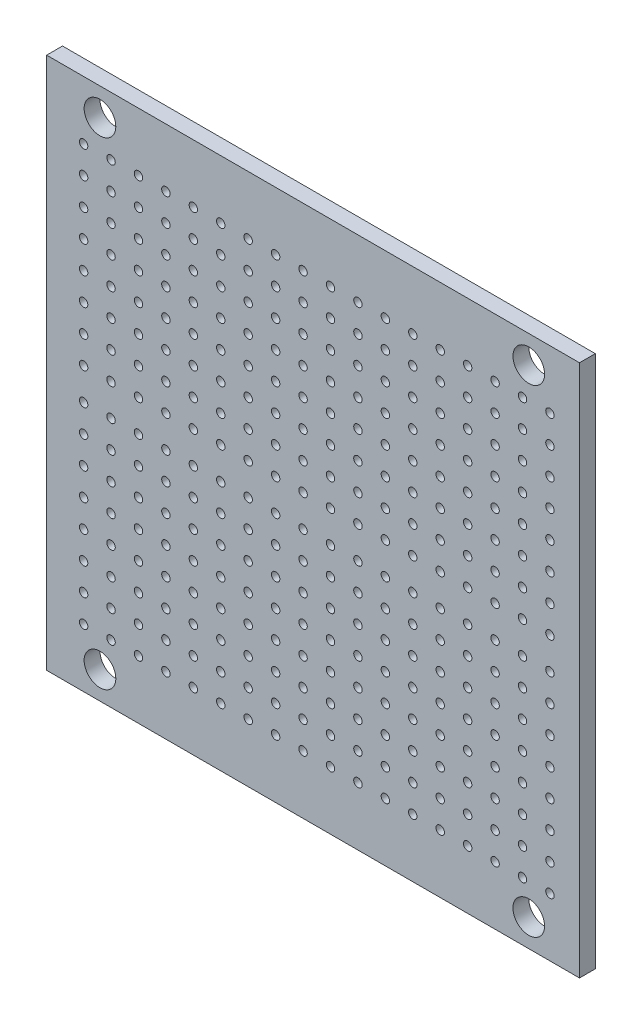
SolidWorks part; units mm, degrees
ref_plane "Front Plane" through (0, 0, 0) normal (0, 0, 1) x (1, 0, 0)
ref_plane "Top Plane" through (0, 0, 0) normal (0, 1, 0) x (1, 0, 0)
ref_plane "Right Plane" through (0, 0, 0) normal (1, 0, 0) x (0, 0, -1)
sketch "Sketch1" plane through (0, 0, 0) normal (0, 0, 1) x (1, 0, 0)
  line L0 (0, 0) -> (25.5, 0) construction
  line L2 (-25, -25.25) -> (-25, 25.25)
  line L3 (-25, 25.25) -> (25.5, 25.25)
  line L4 (25.5, -25.25) -> (25.5, 25.25)
  line L5 (0, 0) -> (-25, 0) construction
  line L6 (-25, -25.25) -> (25.5, -25.25)
  circle A0 centre (-19.95, 22.65) radius 1.5
  circle A1 centre (20.6923, 22.65) radius 1.5
  circle A4 centre (22.7, 19.71) radius 0.4
  circle A5 centre (20.1, 19.71) radius 0.4
  circle A6 centre (17.5, 19.71) radius 0.4
  circle A7 centre (14.9, 19.71) radius 0.4
  circle A8 centre (12.3, 19.71) radius 0.4
  circle A9 centre (9.7, 19.71) radius 0.4
  circle A10 centre (7.1, 19.71) radius 0.4
  circle A11 centre (4.5, 19.71) radius 0.4
  circle A12 centre (1.9, 19.71) radius 0.4
  circle A13 centre (-0.7, 19.71) radius 0.4
  circle A14 centre (-3.3, 19.71) radius 0.4
  circle A15 centre (-5.9, 19.71) radius 0.4
  circle A16 centre (-8.5, 19.71) radius 0.4
  circle A17 centre (-11.1, 19.71) radius 0.4
  circle A18 centre (-13.7, 19.71) radius 0.4
  circle A19 centre (-16.3, 19.71) radius 0.4
  circle A20 centre (-18.9, 19.71) radius 0.4
  circle A21 centre (-21.5, 19.71) radius 0.4
  circle A22 centre (20.1, 17.11) radius 0.4
  circle A23 centre (17.5, 17.11) radius 0.4
  circle A24 centre (14.9, 17.11) radius 0.4
  circle A25 centre (12.3, 17.11) radius 0.4
  circle A26 centre (9.7, 17.11) radius 0.4
  circle A27 centre (7.1, 17.11) radius 0.4
  circle A28 centre (4.5, 17.11) radius 0.4
  circle A29 centre (1.9, 17.11) radius 0.4
  circle A30 centre (-0.7, 17.11) radius 0.4
  circle A31 centre (-3.3, 17.11) radius 0.4
  circle A32 centre (-5.9, 17.11) radius 0.4
  circle A33 centre (-8.5, 17.11) radius 0.4
  circle A34 centre (-11.1, 17.11) radius 0.4
  circle A35 centre (-13.7, 17.11) radius 0.4
  circle A36 centre (-16.3, 17.11) radius 0.4
  circle A37 centre (-18.9, 17.11) radius 0.4
  circle A38 centre (-21.5, 17.11) radius 0.4
  circle A39 centre (20.1, 14.51) radius 0.4
  circle A40 centre (17.5, 14.51) radius 0.4
  circle A41 centre (14.9, 14.51) radius 0.4
  circle A42 centre (12.3, 14.51) radius 0.4
  circle A43 centre (9.7, 14.51) radius 0.4
  circle A44 centre (7.1, 14.51) radius 0.4
  circle A45 centre (4.5, 14.51) radius 0.4
  circle A46 centre (1.9, 14.51) radius 0.4
  circle A47 centre (-0.7, 14.51) radius 0.4
  circle A48 centre (-3.3, 14.51) radius 0.4
  circle A49 centre (-5.9, 14.51) radius 0.4
  circle A50 centre (-8.5, 14.51) radius 0.4
  circle A51 centre (-11.1, 14.51) radius 0.4
  circle A52 centre (-13.7, 14.51) radius 0.4
  circle A53 centre (-16.3, 14.51) radius 0.4
  circle A54 centre (-18.9, 14.51) radius 0.4
  circle A55 centre (-21.5, 14.51) radius 0.4
  circle A56 centre (20.1, 11.91) radius 0.4
  circle A57 centre (17.5, 11.91) radius 0.4
  circle A58 centre (14.9, 11.91) radius 0.4
  circle A59 centre (12.3, 11.91) radius 0.4
  circle A60 centre (9.7, 11.91) radius 0.4
  circle A61 centre (7.1, 11.91) radius 0.4
  circle A62 centre (4.5, 11.91) radius 0.4
  circle A63 centre (1.9, 11.91) radius 0.4
  circle A64 centre (-0.7, 11.91) radius 0.4
  circle A65 centre (-3.3, 11.91) radius 0.4
  circle A66 centre (-5.9, 11.91) radius 0.4
  circle A67 centre (-8.5, 11.91) radius 0.4
  circle A68 centre (-11.1, 11.91) radius 0.4
  circle A69 centre (-13.7, 11.91) radius 0.4
  circle A70 centre (-16.3, 11.91) radius 0.4
  circle A71 centre (-18.9, 11.91) radius 0.4
  circle A72 centre (-21.5, 11.91) radius 0.4
  circle A73 centre (20.1, 9.31) radius 0.4
  circle A74 centre (17.5, 9.31) radius 0.4
  circle A75 centre (14.9, 9.31) radius 0.4
  circle A76 centre (12.3, 9.31) radius 0.4
  circle A77 centre (9.7, 9.31) radius 0.4
  circle A78 centre (7.1, 9.31) radius 0.4
  circle A79 centre (4.5, 9.31) radius 0.4
  circle A80 centre (1.9, 9.31) radius 0.4
  circle A81 centre (-0.7, 9.31) radius 0.4
  circle A82 centre (-3.3, 9.31) radius 0.4
  circle A83 centre (-5.9, 9.31) radius 0.4
  circle A84 centre (-8.5, 9.31) radius 0.4
  circle A85 centre (-11.1, 9.31) radius 0.4
  circle A86 centre (-13.7, 9.31) radius 0.4
  circle A87 centre (-16.3, 9.31) radius 0.4
  circle A88 centre (-18.9, 9.31) radius 0.4
  circle A89 centre (-21.5, 9.31) radius 0.4
  circle A90 centre (20.1, 6.71) radius 0.4
  circle A91 centre (17.5, 6.71) radius 0.4
  circle A92 centre (14.9, 6.71) radius 0.4
  circle A93 centre (12.3, 6.71) radius 0.4
  circle A94 centre (9.7, 6.71) radius 0.4
  circle A95 centre (7.1, 6.71) radius 0.4
  circle A96 centre (4.5, 6.71) radius 0.4
  circle A97 centre (1.9, 6.71) radius 0.4
  circle A98 centre (-0.7, 6.71) radius 0.4
  circle A99 centre (-3.3, 6.71) radius 0.4
  circle A100 centre (-5.9, 6.71) radius 0.4
  circle A101 centre (-8.5, 6.71) radius 0.4
  circle A102 centre (-11.1, 6.71) radius 0.4
  circle A103 centre (-13.7, 6.71) radius 0.4
  circle A104 centre (-16.3, 6.71) radius 0.4
  circle A105 centre (-18.9, 6.71) radius 0.4
  circle A106 centre (-21.5, 6.71) radius 0.4
  circle A107 centre (20.1, 4.11) radius 0.4
  circle A108 centre (17.5, 4.11) radius 0.4
  circle A109 centre (14.9, 4.11) radius 0.4
  circle A110 centre (12.3, 4.11) radius 0.4
  circle A111 centre (9.7, 4.11) radius 0.4
  circle A112 centre (7.1, 4.11) radius 0.4
  circle A113 centre (4.5, 4.11) radius 0.4
  circle A114 centre (1.9, 4.11) radius 0.4
  circle A115 centre (-0.7, 4.11) radius 0.4
  circle A116 centre (-3.3, 4.11) radius 0.4
  circle A117 centre (-5.9, 4.11) radius 0.4
  circle A118 centre (-8.5, 4.11) radius 0.4
  circle A119 centre (-11.1, 4.11) radius 0.4
  circle A120 centre (-13.7, 4.11) radius 0.4
  circle A121 centre (-16.3, 4.11) radius 0.4
  circle A122 centre (-18.9, 4.11) radius 0.4
  circle A123 centre (-21.5, 4.11) radius 0.4
  circle A124 centre (20.1, 1.51) radius 0.4
  circle A125 centre (17.5, 1.51) radius 0.4
  circle A126 centre (14.9, 1.51) radius 0.4
  circle A127 centre (12.3, 1.51) radius 0.4
  circle A128 centre (9.7, 1.51) radius 0.4
  circle A129 centre (7.1, 1.51) radius 0.4
  circle A130 centre (4.5, 1.51) radius 0.4
  circle A131 centre (1.9, 1.51) radius 0.4
  circle A132 centre (-0.7, 1.51) radius 0.4
  circle A133 centre (-3.3, 1.51) radius 0.4
  circle A134 centre (-5.9, 1.51) radius 0.4
  circle A135 centre (-8.5, 1.51) radius 0.4
  circle A136 centre (-11.1, 1.51) radius 0.4
  circle A137 centre (-13.7, 1.51) radius 0.4
  circle A138 centre (-16.3, 1.51) radius 0.4
  circle A139 centre (-18.9, 1.51) radius 0.4
  circle A140 centre (-21.5, 1.51) radius 0.4
  circle A413 centre (22.7, 17.11) radius 0.4
  circle A414 centre (22.7, 14.51) radius 0.4
  circle A415 centre (22.7, 11.91) radius 0.4
  circle A416 centre (22.7, 9.31) radius 0.4
  circle A417 centre (22.7, 6.71) radius 0.4
  circle A418 centre (22.7, 4.11) radius 0.4
  circle A419 centre (22.7, 1.51) radius 0.4
  circle A436 centre (-18.9, -27.09) radius 0.4 [skipped]
  circle A437 centre (-21.5, -27.09) radius 0.4 [skipped]
  circle A438 centre (20.1, -29.69) radius 0.4 [skipped]
  circle A439 centre (17.5, -29.69) radius 0.4 [skipped]
  circle A440 centre (14.9, -29.69) radius 0.4 [skipped]
  circle A441 centre (12.3, -29.69) radius 0.4 [skipped]
  circle A442 centre (9.7, -29.69) radius 0.4 [skipped]
  circle A443 centre (7.1, -29.69) radius 0.4 [skipped]
  circle A444 centre (4.5, -29.69) radius 0.4 [skipped]
  circle A445 centre (1.9, -29.69) radius 0.4 [skipped]
  circle A446 centre (-0.7, -29.69) radius 0.4 [skipped]
  circle A447 centre (-3.3, -29.69) radius 0.4 [skipped]
  circle A448 centre (-5.9, -29.69) radius 0.4 [skipped]
  circle A449 centre (-8.5, -29.69) radius 0.4 [skipped]
  circle A450 centre (-11.1, -29.69) radius 0.4 [skipped]
  circle A451 centre (-13.7, -29.69) radius 0.4 [skipped]
  circle A452 centre (-16.3, -29.69) radius 0.4 [skipped]
  circle A453 centre (-18.9, -29.69) radius 0.4 [skipped]
  circle A454 centre (-21.5, -29.69) radius 0.4 [skipped]
  circle A455 centre (20.1, -32.29) radius 0.4 [skipped]
  circle A456 centre (17.5, -32.29) radius 0.4 [skipped]
  circle A457 centre (14.9, -32.29) radius 0.4 [skipped]
  circle A458 centre (12.3, -32.29) radius 0.4 [skipped]
  circle A459 centre (9.7, -32.29) radius 0.4 [skipped]
  circle A460 centre (7.1, -32.29) radius 0.4 [skipped]
  circle A461 centre (4.5, -32.29) radius 0.4 [skipped]
  circle A462 centre (1.9, -32.29) radius 0.4 [skipped]
  circle A463 centre (-0.7, -32.29) radius 0.4 [skipped]
  circle A464 centre (-3.3, -32.29) radius 0.4 [skipped]
  circle A465 centre (-5.9, -32.29) radius 0.4 [skipped]
  circle A466 centre (-8.5, -32.29) radius 0.4 [skipped]
  circle A467 centre (-11.1, -32.29) radius 0.4 [skipped]
  circle A468 centre (-13.7, -32.29) radius 0.4 [skipped]
  circle A469 centre (-16.3, -32.29) radius 0.4 [skipped]
  circle A470 centre (-18.9, -32.29) radius 0.4 [skipped]
  circle A471 centre (-21.5, -32.29) radius 0.4 [skipped]
  circle A472 centre (20.1, -34.89) radius 0.4 [skipped]
  circle A473 centre (17.5, -34.89) radius 0.4 [skipped]
  circle A474 centre (14.9, -34.89) radius 0.4 [skipped]
  circle A475 centre (12.3, -34.89) radius 0.4 [skipped]
  circle A476 centre (9.7, -34.89) radius 0.4 [skipped]
  circle A477 centre (7.1, -34.89) radius 0.4 [skipped]
  circle A478 centre (4.5, -34.89) radius 0.4 [skipped]
  circle A479 centre (1.9, -34.89) radius 0.4 [skipped]
  circle A480 centre (-0.7, -34.89) radius 0.4 [skipped]
  circle A481 centre (-3.3, -34.89) radius 0.4 [skipped]
  circle A482 centre (-5.9, -34.89) radius 0.4 [skipped]
  circle A483 centre (-8.5, -34.89) radius 0.4 [skipped]
  circle A484 centre (-11.1, -34.89) radius 0.4 [skipped]
  circle A485 centre (-13.7, -34.89) radius 0.4 [skipped]
  circle A486 centre (-16.3, -34.89) radius 0.4 [skipped]
  circle A487 centre (-18.9, -34.89) radius 0.4 [skipped]
  circle A488 centre (-21.5, -34.89) radius 0.4 [skipped]
  circle A489 centre (20.1, -37.49) radius 0.4 [skipped]
  circle A490 centre (17.5, -37.49) radius 0.4 [skipped]
  circle A491 centre (14.9, -37.49) radius 0.4 [skipped]
  circle A492 centre (12.3, -37.49) radius 0.4 [skipped]
  circle A493 centre (9.7, -37.49) radius 0.4 [skipped]
  circle A494 centre (7.1, -37.49) radius 0.4 [skipped]
  circle A495 centre (4.5, -37.49) radius 0.4 [skipped]
  circle A496 centre (1.9, -37.49) radius 0.4 [skipped]
  circle A497 centre (-0.7, -37.49) radius 0.4 [skipped]
  circle A498 centre (-3.3, -37.49) radius 0.4 [skipped]
  circle A499 centre (-5.9, -37.49) radius 0.4 [skipped]
  circle A500 centre (-8.5, -37.49) radius 0.4 [skipped]
  circle A501 centre (-11.1, -37.49) radius 0.4 [skipped]
  circle A502 centre (-13.7, -37.49) radius 0.4 [skipped]
  circle A503 centre (-16.3, -37.49) radius 0.4 [skipped]
  circle A504 centre (-18.9, -37.49) radius 0.4 [skipped]
  circle A505 centre (-21.5, -37.49) radius 0.4 [skipped]
  circle A506 centre (20.1, -40.09) radius 0.4 [skipped]
  circle A507 centre (17.5, -40.09) radius 0.4 [skipped]
  circle A508 centre (14.9, -40.09) radius 0.4 [skipped]
  circle A509 centre (12.3, -40.09) radius 0.4 [skipped]
  circle A510 centre (9.7, -40.09) radius 0.4 [skipped]
  circle A511 centre (7.1, -40.09) radius 0.4 [skipped]
  circle A512 centre (4.5, -40.09) radius 0.4 [skipped]
  circle A513 centre (1.9, -40.09) radius 0.4 [skipped]
  circle A514 centre (-0.7, -40.09) radius 0.4 [skipped]
  circle A515 centre (22.7, -29.69) radius 0.4 [skipped]
  circle A516 centre (22.7, -32.29) radius 0.4 [skipped]
  circle A517 centre (22.7, -34.89) radius 0.4 [skipped]
  circle A518 centre (22.7, -37.49) radius 0.4 [skipped]
  circle A519 centre (22.7, -40.09) radius 0.4 [skipped]
  circle A520 centre (-3.3, -40.09) radius 0.4 [skipped]
  circle A521 centre (-5.9, -40.09) radius 0.4 [skipped]
  circle A522 centre (-8.5, -40.09) radius 0.4 [skipped]
  circle A523 centre (-11.1, -40.09) radius 0.4 [skipped]
  circle A524 centre (-13.7, -40.09) radius 0.4 [skipped]
  circle A525 centre (-16.3, -40.09) radius 0.4 [skipped]
  circle A526 centre (-18.9, -40.09) radius 0.4 [skipped]
  circle A527 centre (-21.5, -40.09) radius 0.4 [skipped]
  circle A528 centre (20.1, -27.09) radius 0.4 [skipped]
  circle A529 centre (17.5, -27.09) radius 0.4 [skipped]
  circle A530 centre (14.9, -27.09) radius 0.4 [skipped]
  circle A531 centre (12.3, -27.09) radius 0.4 [skipped]
  circle A532 centre (9.7, -27.09) radius 0.4 [skipped]
  circle A533 centre (7.1, -27.09) radius 0.4 [skipped]
  circle A534 centre (4.5, -27.09) radius 0.4 [skipped]
  circle A535 centre (1.9, -27.09) radius 0.4 [skipped]
  circle A536 centre (-0.7, -27.09) radius 0.4 [skipped]
  circle A537 centre (-3.3, -27.09) radius 0.4 [skipped]
  circle A538 centre (-5.9, -27.09) radius 0.4 [skipped]
  circle A539 centre (-8.5, -27.09) radius 0.4 [skipped]
  circle A540 centre (-11.1, -27.09) radius 0.4 [skipped]
  circle A541 centre (-13.7, -27.09) radius 0.4 [skipped]
  circle A542 centre (-16.3, -27.09) radius 0.4 [skipped]
  circle A543 centre (22.7, -27.09) radius 0.4 [skipped]
  circle A544 centre (20.1, -1.09) radius 0.4 [skipped]
  circle A545 centre (17.5, -1.09) radius 0.4 [skipped]
  circle A546 centre (14.9, -1.09) radius 0.4 [skipped]
  circle A547 centre (12.3, -1.09) radius 0.4 [skipped]
  circle A548 centre (9.7, -1.09) radius 0.4 [skipped]
  circle A549 centre (7.1, -1.09) radius 0.4 [skipped]
  circle A550 centre (4.5, -1.09) radius 0.4 [skipped]
  circle A551 centre (1.9, -1.09) radius 0.4 [skipped]
  circle A552 centre (-0.7, -1.09) radius 0.4 [skipped]
  circle A553 centre (-3.3, -1.09) radius 0.4 [skipped]
  circle A554 centre (-5.9, -1.09) radius 0.4 [skipped]
  circle A555 centre (-8.5, -1.09) radius 0.4 [skipped]
  circle A556 centre (-11.1, -1.09) radius 0.4 [skipped]
  circle A557 centre (-13.7, -1.09) radius 0.4 [skipped]
  circle A558 centre (-16.3, -1.09) radius 0.4 [skipped]
  circle A559 centre (-18.9, -1.09) radius 0.4 [skipped]
  circle A560 centre (-21.5, -1.09) radius 0.4 [skipped]
  circle A561 centre (20.1, -3.69) radius 0.4 [skipped]
  circle A562 centre (17.5, -3.69) radius 0.4 [skipped]
  circle A563 centre (14.9, -3.69) radius 0.4 [skipped]
  circle A564 centre (12.3, -3.69) radius 0.4 [skipped]
  circle A565 centre (9.7, -3.69) radius 0.4 [skipped]
  circle A566 centre (7.1, -3.69) radius 0.4 [skipped]
  circle A567 centre (4.5, -3.69) radius 0.4 [skipped]
  circle A568 centre (1.9, -3.69) radius 0.4 [skipped]
  circle A569 centre (-0.7, -3.69) radius 0.4 [skipped]
  circle A570 centre (-3.3, -3.69) radius 0.4 [skipped]
  circle A571 centre (-5.9, -3.69) radius 0.4 [skipped]
  circle A572 centre (-8.5, -3.69) radius 0.4 [skipped]
  circle A573 centre (-11.1, -3.69) radius 0.4 [skipped]
  circle A574 centre (-13.7, -3.69) radius 0.4 [skipped]
  circle A575 centre (-16.3, -3.69) radius 0.4 [skipped]
  circle A576 centre (-18.9, -3.69) radius 0.4 [skipped]
  circle A577 centre (-21.5, -3.69) radius 0.4 [skipped]
  circle A578 centre (20.1, -6.29) radius 0.4 [skipped]
  circle A579 centre (17.5, -6.29) radius 0.4 [skipped]
  circle A580 centre (14.9, -6.29) radius 0.4 [skipped]
  circle A581 centre (12.3, -6.29) radius 0.4 [skipped]
  circle A582 centre (9.7, -6.29) radius 0.4 [skipped]
  circle A583 centre (7.1, -6.29) radius 0.4 [skipped]
  circle A584 centre (4.5, -6.29) radius 0.4 [skipped]
  circle A585 centre (1.9, -6.29) radius 0.4 [skipped]
  circle A586 centre (-0.7, -6.29) radius 0.4 [skipped]
  circle A587 centre (-3.3, -6.29) radius 0.4 [skipped]
  circle A588 centre (-5.9, -6.29) radius 0.4 [skipped]
  circle A589 centre (-8.5, -6.29) radius 0.4 [skipped]
  circle A590 centre (-11.1, -6.29) radius 0.4 [skipped]
  circle A591 centre (-13.7, -6.29) radius 0.4 [skipped]
  circle A592 centre (-16.3, -6.29) radius 0.4 [skipped]
  circle A593 centre (-18.9, -6.29) radius 0.4 [skipped]
  circle A594 centre (-21.5, -6.29) radius 0.4 [skipped]
  circle A595 centre (20.1, -8.89) radius 0.4 [skipped]
  circle A596 centre (17.5, -8.89) radius 0.4 [skipped]
  circle A597 centre (14.9, -8.89) radius 0.4 [skipped]
  circle A598 centre (12.3, -8.89) radius 0.4 [skipped]
  circle A599 centre (9.7, -8.89) radius 0.4 [skipped]
  circle A600 centre (7.1, -8.89) radius 0.4 [skipped]
  circle A601 centre (4.5, -8.89) radius 0.4 [skipped]
  circle A602 centre (1.9, -8.89) radius 0.4 [skipped]
  circle A603 centre (-0.7, -8.89) radius 0.4 [skipped]
  circle A604 centre (-3.3, -8.89) radius 0.4 [skipped]
  circle A605 centre (-5.9, -8.89) radius 0.4 [skipped]
  circle A606 centre (-8.5, -8.89) radius 0.4 [skipped]
  circle A607 centre (-11.1, -8.89) radius 0.4 [skipped]
  circle A608 centre (-13.7, -8.89) radius 0.4 [skipped]
  circle A609 centre (-16.3, -8.89) radius 0.4 [skipped]
  circle A610 centre (-18.9, -8.89) radius 0.4 [skipped]
  circle A611 centre (-21.5, -8.89) radius 0.4 [skipped]
  circle A612 centre (20.1, -11.49) radius 0.4 [skipped]
  circle A613 centre (17.5, -11.49) radius 0.4 [skipped]
  circle A614 centre (14.9, -11.49) radius 0.4 [skipped]
  circle A615 centre (12.3, -11.49) radius 0.4 [skipped]
  circle A616 centre (9.7, -11.49) radius 0.4 [skipped]
  circle A617 centre (7.1, -11.49) radius 0.4 [skipped]
  circle A618 centre (4.5, -11.49) radius 0.4 [skipped]
  circle A619 centre (1.9, -11.49) radius 0.4 [skipped]
  circle A620 centre (-0.7, -11.49) radius 0.4 [skipped]
  circle A621 centre (-3.3, -11.49) radius 0.4 [skipped]
  circle A622 centre (-5.9, -11.49) radius 0.4 [skipped]
  circle A623 centre (-8.5, -11.49) radius 0.4 [skipped]
  circle A624 centre (-11.1, -11.49) radius 0.4 [skipped]
  circle A625 centre (-13.7, -11.49) radius 0.4 [skipped]
  circle A626 centre (-16.3, -11.49) radius 0.4 [skipped]
  circle A627 centre (-18.9, -11.49) radius 0.4 [skipped]
  circle A628 centre (-21.5, -11.49) radius 0.4 [skipped]
  circle A629 centre (20.1, -14.09) radius 0.4 [skipped]
  circle A630 centre (17.5, -14.09) radius 0.4 [skipped]
  circle A631 centre (14.9, -14.09) radius 0.4 [skipped]
  circle A632 centre (12.3, -14.09) radius 0.4 [skipped]
  circle A633 centre (9.7, -14.09) radius 0.4 [skipped]
  circle A634 centre (7.1, -14.09) radius 0.4 [skipped]
  circle A635 centre (4.5, -14.09) radius 0.4 [skipped]
  circle A636 centre (1.9, -14.09) radius 0.4 [skipped]
  circle A637 centre (-0.7, -14.09) radius 0.4 [skipped]
  circle A638 centre (-3.3, -14.09) radius 0.4 [skipped]
  circle A639 centre (-5.9, -14.09) radius 0.4 [skipped]
  circle A640 centre (-8.5, -14.09) radius 0.4 [skipped]
  circle A641 centre (-11.1, -14.09) radius 0.4 [skipped]
  circle A642 centre (-13.7, -14.09) radius 0.4 [skipped]
  circle A643 centre (-16.3, -14.09) radius 0.4 [skipped]
  circle A644 centre (-18.9, -14.09) radius 0.4 [skipped]
  circle A645 centre (-21.5, -14.09) radius 0.4 [skipped]
  circle A646 centre (20.1, -16.69) radius 0.4 [skipped]
  circle A647 centre (17.5, -16.69) radius 0.4 [skipped]
  circle A648 centre (14.9, -16.69) radius 0.4 [skipped]
  circle A649 centre (12.3, -16.69) radius 0.4 [skipped]
  circle A650 centre (9.7, -16.69) radius 0.4 [skipped]
  circle A651 centre (7.1, -16.69) radius 0.4 [skipped]
  circle A652 centre (4.5, -16.69) radius 0.4 [skipped]
  circle A653 centre (1.9, -16.69) radius 0.4 [skipped]
  circle A654 centre (-0.7, -16.69) radius 0.4 [skipped]
  circle A655 centre (-3.3, -16.69) radius 0.4 [skipped]
  circle A656 centre (-5.9, -16.69) radius 0.4 [skipped]
  circle A657 centre (-8.5, -16.69) radius 0.4 [skipped]
  circle A658 centre (-11.1, -16.69) radius 0.4 [skipped]
  circle A659 centre (-13.7, -16.69) radius 0.4 [skipped]
  circle A660 centre (-16.3, -16.69) radius 0.4 [skipped]
  circle A661 centre (-18.9, -16.69) radius 0.4 [skipped]
  circle A662 centre (-21.5, -16.69) radius 0.4 [skipped]
  circle A663 centre (20.1, -19.29) radius 0.4 [skipped]
  circle A664 centre (17.5, -19.29) radius 0.4 [skipped]
  circle A665 centre (14.9, -19.29) radius 0.4 [skipped]
  circle A666 centre (12.3, -19.29) radius 0.4 [skipped]
  circle A667 centre (9.7, -19.29) radius 0.4 [skipped]
  circle A668 centre (7.1, -19.29) radius 0.4 [skipped]
  circle A669 centre (4.5, -19.29) radius 0.4 [skipped]
  circle A670 centre (1.9, -19.29) radius 0.4 [skipped]
  circle A671 centre (-0.7, -19.29) radius 0.4 [skipped]
  circle A672 centre (-3.3, -19.29) radius 0.4 [skipped]
  circle A673 centre (-5.9, -19.29) radius 0.4 [skipped]
  circle A674 centre (-8.5, -19.29) radius 0.4 [skipped]
  circle A675 centre (-11.1, -19.29) radius 0.4 [skipped]
  circle A676 centre (-13.7, -19.29) radius 0.4 [skipped]
  circle A677 centre (-16.3, -19.29) radius 0.4 [skipped]
  circle A678 centre (-18.9, -19.29) radius 0.4 [skipped]
  circle A679 centre (-21.5, -19.29) radius 0.4 [skipped]
  circle A680 centre (20.1, -21.89) radius 0.4 [skipped]
  circle A681 centre (17.5, -21.89) radius 0.4 [skipped]
  circle A682 centre (14.9, -21.89) radius 0.4 [skipped]
  circle A683 centre (12.3, -21.89) radius 0.4 [skipped]
  circle A684 centre (9.7, -21.89) radius 0.4 [skipped]
  circle A685 centre (7.1, -21.89) radius 0.4 [skipped]
  circle A686 centre (4.5, -21.89) radius 0.4 [skipped]
  circle A687 centre (1.9, -21.89) radius 0.4 [skipped]
  circle A688 centre (-0.7, -21.89) radius 0.4 [skipped]
  circle A689 centre (-3.3, -21.89) radius 0.4 [skipped]
  circle A690 centre (-5.9, -21.89) radius 0.4 [skipped]
  circle A691 centre (-8.5, -21.89) radius 0.4 [skipped]
  circle A692 centre (-11.1, -21.89) radius 0.4 [skipped]
  circle A693 centre (-13.7, -21.89) radius 0.4 [skipped]
  circle A694 centre (-16.3, -21.89) radius 0.4 [skipped]
  circle A695 centre (-18.9, -21.89) radius 0.4 [skipped]
  circle A696 centre (-21.5, -21.89) radius 0.4 [skipped]
  circle A697 centre (20.1, -24.49) radius 0.4 [skipped]
  circle A698 centre (17.5, -24.49) radius 0.4 [skipped]
  circle A699 centre (14.9, -24.49) radius 0.4 [skipped]
  circle A700 centre (12.3, -24.49) radius 0.4 [skipped]
  circle A701 centre (9.7, -24.49) radius 0.4 [skipped]
  circle A702 centre (7.1, -24.49) radius 0.4 [skipped]
  circle A703 centre (4.5, -24.49) radius 0.4 [skipped]
  circle A704 centre (1.9, -24.49) radius 0.4 [skipped]
  circle A705 centre (-0.7, -24.49) radius 0.4 [skipped]
  circle A706 centre (-3.3, -24.49) radius 0.4 [skipped]
  circle A707 centre (-5.9, -24.49) radius 0.4 [skipped]
  circle A708 centre (-8.5, -24.49) radius 0.4 [skipped]
  circle A709 centre (-11.1, -24.49) radius 0.4 [skipped]
  circle A710 centre (-13.7, -24.49) radius 0.4 [skipped]
  circle A711 centre (-16.3, -24.49) radius 0.4 [skipped]
  circle A712 centre (-18.9, -24.49) radius 0.4 [skipped]
  circle A713 centre (-21.5, -24.49) radius 0.4 [skipped]
  circle A714 centre (22.7, -1.09) radius 0.4 [skipped]
  circle A715 centre (22.7, -3.69) radius 0.4 [skipped]
  circle A716 centre (22.7, -6.29) radius 0.4 [skipped]
  circle A717 centre (22.7, -8.89) radius 0.4 [skipped]
  circle A718 centre (22.7, -11.49) radius 0.4 [skipped]
  circle A719 centre (22.7, -14.09) radius 0.4 [skipped]
  circle A720 centre (22.7, -16.69) radius 0.4 [skipped]
  circle A721 centre (22.7, -19.29) radius 0.4 [skipped]
  circle A722 centre (22.7, -21.89) radius 0.4 [skipped]
  circle A723 centre (22.7, -24.49) radius 0.4 [skipped]
  circle A724 centre (22.7, -1.51) radius 0.4
  circle A725 centre (22.7, -4.11) radius 0.4
  circle A726 centre (22.7, -6.71) radius 0.4
  circle A727 centre (22.7, -9.31) radius 0.4
  circle A728 centre (22.7, -11.91) radius 0.4
  circle A729 centre (22.7, -14.51) radius 0.4
  circle A730 centre (22.7, -17.11) radius 0.4
  circle A731 centre (-21.5, -1.51) radius 0.4
  circle A732 centre (-18.9, -1.51) radius 0.4
  circle A733 centre (-16.3, -1.51) radius 0.4
  circle A734 centre (-13.7, -1.51) radius 0.4
  circle A735 centre (-11.1, -1.51) radius 0.4
  circle A736 centre (-8.5, -1.51) radius 0.4
  circle A737 centre (-5.9, -1.51) radius 0.4
  circle A738 centre (-3.3, -1.51) radius 0.4
  circle A739 centre (-0.7, -1.51) radius 0.4
  circle A740 centre (1.9, -1.51) radius 0.4
  circle A741 centre (4.5, -1.51) radius 0.4
  circle A742 centre (7.1, -1.51) radius 0.4
  circle A743 centre (9.7, -1.51) radius 0.4
  circle A744 centre (12.3, -1.51) radius 0.4
  circle A745 centre (14.9, -1.51) radius 0.4
  circle A746 centre (17.5, -1.51) radius 0.4
  circle A747 centre (20.1, -1.51) radius 0.4
  circle A748 centre (-21.5, -4.11) radius 0.4
  circle A749 centre (-18.9, -4.11) radius 0.4
  circle A750 centre (-16.3, -4.11) radius 0.4
  circle A751 centre (-13.7, -4.11) radius 0.4
  circle A752 centre (-11.1, -4.11) radius 0.4
  circle A753 centre (-8.5, -4.11) radius 0.4
  circle A754 centre (-5.9, -4.11) radius 0.4
  circle A755 centre (-3.3, -4.11) radius 0.4
  circle A756 centre (-0.7, -4.11) radius 0.4
  circle A757 centre (1.9, -4.11) radius 0.4
  circle A758 centre (4.5, -4.11) radius 0.4
  circle A759 centre (7.1, -4.11) radius 0.4
  circle A760 centre (9.7, -4.11) radius 0.4
  circle A761 centre (12.3, -4.11) radius 0.4
  circle A762 centre (14.9, -4.11) radius 0.4
  circle A763 centre (17.5, -4.11) radius 0.4
  circle A764 centre (20.1, -4.11) radius 0.4
  circle A765 centre (-21.5, -6.71) radius 0.4
  circle A766 centre (-18.9, -6.71) radius 0.4
  circle A767 centre (-16.3, -6.71) radius 0.4
  circle A768 centre (-13.7, -6.71) radius 0.4
  circle A769 centre (-11.1, -6.71) radius 0.4
  circle A770 centre (-8.5, -6.71) radius 0.4
  circle A771 centre (-5.9, -6.71) radius 0.4
  circle A772 centre (-3.3, -6.71) radius 0.4
  circle A773 centre (-0.7, -6.71) radius 0.4
  circle A774 centre (1.9, -6.71) radius 0.4
  circle A775 centre (4.5, -6.71) radius 0.4
  circle A776 centre (7.1, -6.71) radius 0.4
  circle A777 centre (9.7, -6.71) radius 0.4
  circle A778 centre (12.3, -6.71) radius 0.4
  circle A779 centre (14.9, -6.71) radius 0.4
  circle A780 centre (17.5, -6.71) radius 0.4
  circle A781 centre (20.1, -6.71) radius 0.4
  circle A782 centre (-21.5, -9.31) radius 0.4
  circle A783 centre (-18.9, -9.31) radius 0.4
  circle A784 centre (-16.3, -9.31) radius 0.4
  circle A785 centre (-13.7, -9.31) radius 0.4
  circle A786 centre (-11.1, -9.31) radius 0.4
  circle A787 centre (-8.5, -9.31) radius 0.4
  circle A788 centre (-5.9, -9.31) radius 0.4
  circle A789 centre (-3.3, -9.31) radius 0.4
  circle A790 centre (-0.7, -9.31) radius 0.4
  circle A791 centre (1.9, -9.31) radius 0.4
  circle A792 centre (4.5, -9.31) radius 0.4
  circle A793 centre (7.1, -9.31) radius 0.4
  circle A794 centre (9.7, -9.31) radius 0.4
  circle A795 centre (12.3, -9.31) radius 0.4
  circle A796 centre (14.9, -9.31) radius 0.4
  circle A797 centre (17.5, -9.31) radius 0.4
  circle A798 centre (20.1, -9.31) radius 0.4
  circle A799 centre (-21.5, -11.91) radius 0.4
  circle A800 centre (-18.9, -11.91) radius 0.4
  circle A801 centre (-16.3, -11.91) radius 0.4
  circle A802 centre (-13.7, -11.91) radius 0.4
  circle A803 centre (-11.1, -11.91) radius 0.4
  circle A804 centre (-8.5, -11.91) radius 0.4
  circle A805 centre (-5.9, -11.91) radius 0.4
  circle A806 centre (-3.3, -11.91) radius 0.4
  circle A807 centre (-0.7, -11.91) radius 0.4
  circle A808 centre (1.9, -11.91) radius 0.4
  circle A809 centre (4.5, -11.91) radius 0.4
  circle A810 centre (7.1, -11.91) radius 0.4
  circle A811 centre (9.7, -11.91) radius 0.4
  circle A812 centre (12.3, -11.91) radius 0.4
  circle A813 centre (14.9, -11.91) radius 0.4
  circle A814 centre (17.5, -11.91) radius 0.4
  circle A815 centre (20.1, -11.91) radius 0.4
  circle A816 centre (-21.5, -14.51) radius 0.4
  circle A817 centre (-18.9, -14.51) radius 0.4
  circle A818 centre (-16.3, -14.51) radius 0.4
  circle A819 centre (-13.7, -14.51) radius 0.4
  circle A820 centre (-11.1, -14.51) radius 0.4
  circle A821 centre (-8.5, -14.51) radius 0.4
  circle A822 centre (-5.9, -14.51) radius 0.4
  circle A823 centre (-3.3, -14.51) radius 0.4
  circle A824 centre (-0.7, -14.51) radius 0.4
  circle A825 centre (1.9, -14.51) radius 0.4
  circle A826 centre (4.5, -14.51) radius 0.4
  circle A827 centre (7.1, -14.51) radius 0.4
  circle A828 centre (9.7, -14.51) radius 0.4
  circle A829 centre (12.3, -14.51) radius 0.4
  circle A830 centre (14.9, -14.51) radius 0.4
  circle A831 centre (17.5, -14.51) radius 0.4
  circle A832 centre (20.1, -14.51) radius 0.4
  circle A833 centre (-21.5, -17.11) radius 0.4
  circle A834 centre (-18.9, -17.11) radius 0.4
  circle A835 centre (-16.3, -17.11) radius 0.4
  circle A836 centre (-13.7, -17.11) radius 0.4
  circle A837 centre (-11.1, -17.11) radius 0.4
  circle A838 centre (-8.5, -17.11) radius 0.4
  circle A839 centre (-5.9, -17.11) radius 0.4
  circle A840 centre (-3.3, -17.11) radius 0.4
  circle A841 centre (-0.7, -17.11) radius 0.4
  circle A842 centre (1.9, -17.11) radius 0.4
  circle A843 centre (4.5, -17.11) radius 0.4
  circle A844 centre (7.1, -17.11) radius 0.4
  circle A845 centre (9.7, -17.11) radius 0.4
  circle A846 centre (12.3, -17.11) radius 0.4
  circle A847 centre (14.9, -17.11) radius 0.4
  circle A848 centre (17.5, -17.11) radius 0.4
  circle A849 centre (20.1, -17.11) radius 0.4
  circle A850 centre (-21.5, -19.71) radius 0.4
  circle A851 centre (-18.9, -19.71) radius 0.4
  circle A852 centre (-16.3, -19.71) radius 0.4
  circle A853 centre (-13.7, -19.71) radius 0.4
  circle A854 centre (-11.1, -19.71) radius 0.4
  circle A855 centre (-8.5, -19.71) radius 0.4
  circle A856 centre (-5.9, -19.71) radius 0.4
  circle A857 centre (-3.3, -19.71) radius 0.4
  circle A858 centre (-0.7, -19.71) radius 0.4
  circle A859 centre (1.9, -19.71) radius 0.4
  circle A860 centre (4.5, -19.71) radius 0.4
  circle A861 centre (7.1, -19.71) radius 0.4
  circle A862 centre (9.7, -19.71) radius 0.4
  circle A863 centre (12.3, -19.71) radius 0.4
  circle A864 centre (14.9, -19.71) radius 0.4
  circle A865 centre (17.5, -19.71) radius 0.4
  circle A866 centre (20.1, -19.71) radius 0.4
  circle A867 centre (22.7, -19.71) radius 0.4
  circle A868 centre (20.6923, -22.65) radius 1.5
  circle A869 centre (-19.95, -22.65) radius 1.5
  point P0 (20.6923, 22.65)
  dimension "D3" = 3
  dimension "D6" = 0.8
  dimension "D2" = 50.5
  dimension "D4" = 2.6
  dimension "D5" = 5.05
  dimension "D7" = 5.54
  dimension "D8" = 2.8
  dimension "D11" = 2.6
  dimension "D12" = 2.6
  dimension "D13" = 50.5
  dimension "D9" = 18
  dimension "D10" = 24
extrude "Boss-Extrude1" add sketch "Sketch1" along normal blind 1.5
scale "Scale4" scale about centroid uniform scaling yes scale factor 1.485
